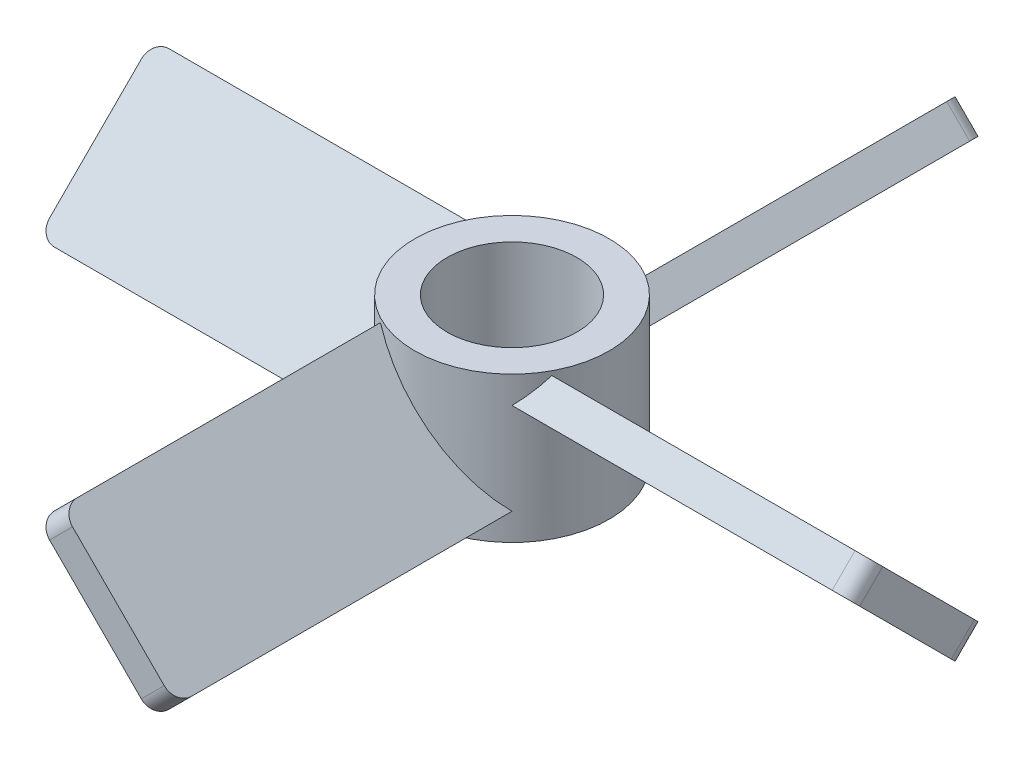
SolidWorks part; units mm, degrees
ref_plane "Alzado" through (0, 0, 0) normal (0, 0, 1) x (1, 0, 0)
ref_plane "Planta" through (0, 0, 0) normal (0, 1, 0) x (1, 0, 0)
ref_plane "Vista lateral" through (0, 0, 0) normal (1, 0, 0) x (0, 0, -1)
sketch "Croquis1" plane through (0, 0, 0) normal (1, 0, 0) x (0, 0, -1)
  line L0 (2.8284, -4.2426) -> (-4.2426, 2.8284)
  line L1 (2.8284, -4.2426) -> (4.2426, -2.8284)
  line L2 (-4.2426, 2.8284) -> (-2.8284, 4.2426)
  line L3 (4.2426, -2.8284) -> (-2.8284, 4.2426)
  line L4 (2.8284, -4.2426) -> (-2.8284, 4.2426) construction
  line L5 (-4.2426, 2.8284) -> (4.2426, -2.8284) construction
  line L6 (0, 0) -> (3.5355, -3.5355) construction
  line L7 (0, 0) -> (12.9754, 0) construction
  point P1 (0, 0)
  dimension "D1" = 45
  dimension "D2" = 2
  dimension "D3" = 10
ref_plane "Plano1" through (21, 0, 0) normal (1, 0, 0) x (0, 0, -1)
sketch "Croquis2" plane through (21, 0, 0) normal (1, 0, 0) x (0, 0, -1)
  line L0 (4.2426, -2.8284) -> (-2.8284, 4.2426)
  line L1 (4.2426, -2.8284) -> (2.8284, -4.2426)
  line L2 (-2.8284, 4.2426) -> (-4.2426, 2.8284)
  line L3 (2.8284, -4.2426) -> (-4.2426, 2.8284)
  line L4 (4.2426, -2.8284) -> (-4.2426, 2.8284) construction
  line L5 (-2.8284, 4.2426) -> (2.8284, -4.2426) construction
  line L6 (0, 0) -> (0.7595, 0) construction
  line L7 (0, 0) -> (3.5355, -3.5355) construction
  point P1 (0, 0)
  dimension "D1" = 2
  dimension "D2" = 10
  dimension "D3" = 45
loft "Recubrir2" add profiles "Croquis1", "Croquis2"
sketch "Croquis3" plane through (0, 0, 0) normal (0, 1, 0) x (1, 0, 0)
  line L0 (10.5, 4.2426) -> (10.5, -4.2426) construction
  line L1 (0, 4.2426) -> (21, 4.2426) construction
  line L2 (0, -4.2426) -> (21, -4.2426) construction
  line L3 (10.5, 0) -> (-2.8604, 0) construction
  circle A0 centre (-4, 0) radius 6
  dimension "D1" = 12
  dimension "D2" = 4
extrude "Saliente-Extruir1" add sketch "Croquis3" along normal mid plane 9
pattern_circular "MatrizC2" count 4 over 360 about axis through (-4, 0, 0) along (0, 1, 0) of "Recubrir2"
sketch "Croquis4" plane through (0, 4.5, 0) normal (0, 1, 0) x (1, 0, 0)
  circle A0 centre (-4, 0) radius 4
  dimension "D1" = 8
extrude "Cortar-Extruir1" cut sketch "Croquis4" against normal up to surface (9 mm away) up to face at (-4, -4.5, 6)
fillet "Redondeo1" radius 1 8 edges
